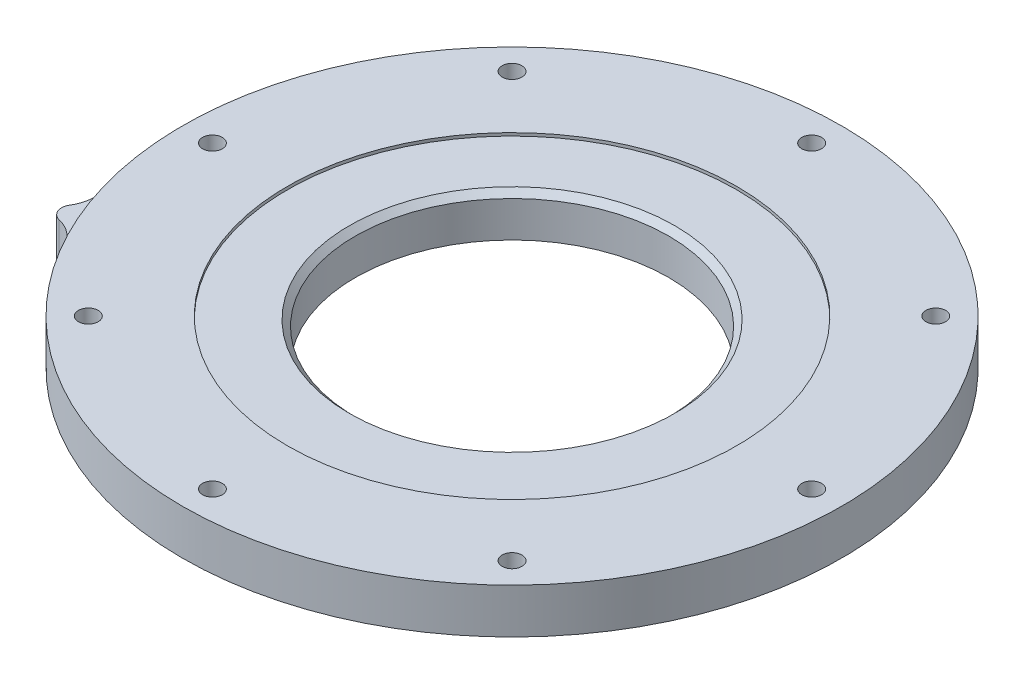
SolidWorks part; units mm, degrees
ref_plane "Front Plane" through (0, 0, 0) normal (0, 0, 1) x (1, 0, 0)
ref_plane "Top Plane" through (0, 0, 0) normal (0, 1, 0) x (1, 0, 0)
ref_plane "Right Plane" through (0, 0, 0) normal (1, 0, 0) x (0, 0, -1)
sketch "Sketch1" plane through (0, 0, 0) normal (0, 1, 0) x (1, 0, 0)
  circle A0 centre (0, 0) radius 55
  circle A1 centre (0, 0) radius 37.5
  circle A2 centre (0, 50) radius 1.65
  circle A3 centre (35.3553, 35.3553) radius 1.65
  circle A4 centre (50, 0) radius 1.65
  circle A5 centre (35.3553, -35.3553) radius 1.65
  circle A6 centre (0, -50) radius 1.65
  circle A7 centre (-35.3553, -35.3553) radius 1.65
  circle A8 centre (-50, 0) radius 1.65
  circle A9 centre (-35.3553, 35.3553) radius 1.65
  point P23 (0, 0)
  dimension "D1" = 110
  dimension "D2" = 75
  dimension "D4" = 3.3
  dimension "D3" = 50
  dimension "D5" = 8
extrude "Boss-Extrude1" add sketch "Sketch1" along normal blind 0.5
sketch "Sketch2" plane through (0, 0, 0) normal (0, -1, 0) x (1, 0, 0)
  line L0 (-51.7373, 21.4303) -> (0, 0) construction
  line L1 (0, 0) -> (0, 50) construction
  circle A0 centre (0, 0) radius 26.15
  circle A1 centre (0, 0) radius 55 construction
  circle A4 centre (0, -50) radius 1.65
  circle A5 centre (0, -50) radius 1.65
  circle A6 centre (35.3553, -35.3553) radius 1.65
  circle A7 centre (35.3553, -35.3553) radius 1.65
  circle A8 centre (50, 0) radius 1.65
  circle A9 centre (50, 0) radius 1.65
  circle A10 centre (35.3553, 35.3553) radius 1.65
  circle A11 centre (35.3553, 35.3553) radius 1.65
  circle A12 centre (0, 50) radius 1.65
  circle A13 centre (0, 50) radius 1.65
  circle A14 centre (-35.3553, 35.3553) radius 1.65
  circle A15 centre (-35.3553, 35.3553) radius 1.65
  circle A16 centre (-50, 0) radius 1.65
  circle A17 centre (-50, 0) radius 1.65
  circle A18 centre (-35.3553, -35.3553) radius 1.65
  circle A19 centre (-35.3553, -35.3553) radius 1.65
  arc A20 (-52.769, 15.5058) -> (-48.2776, 26.3491) centre (0, 0) ccw
  arc A21 (-52.189, 23.3786) -> (-53.4344, 20.372) centre (-51.7373, 21.4303) ccw
  arc A22 (-52.189, 23.3786) -> (-48.2776, 26.3491) centre (-53.5442, 29.2235) ccw
  arc A23 (-53.4344, 20.372) -> (-52.769, 15.5058) centre (-58.5256, 17.1973) cw
  dimension "D1" = 52.3
  dimension "D12" = 4
  dimension "D13" = 6
  dimension "D10" = 67.5
  dimension "D11" = 56
  dimension "D2" = 0
  dimension "D3" = 0
  dimension "D4" = 0
  dimension "D5" = 0
  dimension "D6" = 0
  dimension "D7" = 0
  dimension "D8" = 0
  dimension "D9" = 0
extrude "Boss-Extrude2" add sketch "Sketch2" along normal blind 7
chamfer "Chamfer1" distance 1 angle 45 1 edges at (0, 0, -26.15)
sketch "Sketch3" plane through (0, -7, 0) normal (0, -1, 0) x (1, 0, 0)
  circle A0 centre (-50, 0) radius 1.65 construction
  circle A1 centre (-50, 0) radius 3.65
  circle A3 centre (-35.3553, -35.3553) radius 1.65 construction
  circle A4 centre (0, -50) radius 1.65 construction
  circle A5 centre (35.3553, -35.3553) radius 1.65 construction
  circle A6 centre (50, 0) radius 1.65 construction
  circle A7 centre (35.3553, 35.3553) radius 1.65 construction
  circle A8 centre (0, 50) radius 1.65 construction
  circle A9 centre (-35.3553, 35.3553) radius 1.65 construction
  circle A10 centre (-50, 0) radius 1.65
  circle A11 centre (-35.3553, -35.3553) radius 1.65
  circle A12 centre (0, -50) radius 1.65
  circle A13 centre (35.3553, -35.3553) radius 1.65
  circle A14 centre (50, 0) radius 1.65
  circle A15 centre (35.3553, 35.3553) radius 1.65
  circle A16 centre (0, 50) radius 1.65
  circle A17 centre (-35.3553, 35.3553) radius 1.65
  circle A18 centre (-35.3553, -35.3553) radius 3.65
  circle A19 centre (0, -50) radius 3.65
  circle A20 centre (35.3553, -35.3553) radius 3.65
  circle A21 centre (50, 0) radius 3.65
  circle A22 centre (35.3553, 35.3553) radius 3.65
  circle A23 centre (0, 50) radius 3.65
  circle A24 centre (-35.3553, 35.3553) radius 3.65
  dimension "D1" = 2
extrude "Cut-Extrude1" cut sketch "Sketch3" against normal blind 4
